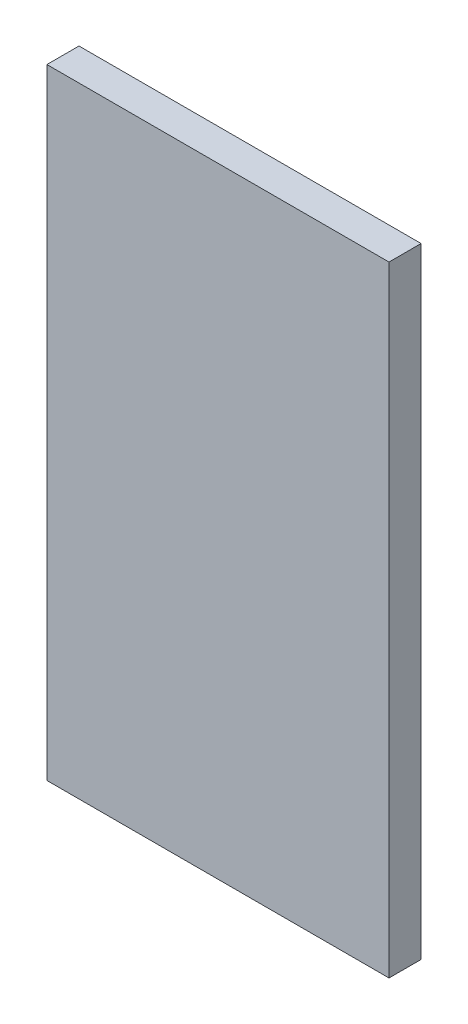
SolidWorks part; units mm, degrees
ref_plane "Plan de face" through (0, 0, 0) normal (0, 0, 1) x (1, 0, 0)
ref_plane "Plan de dessus" through (0, 0, 0) normal (0, 1, 0) x (1, 0, 0)
ref_plane "Plan de droite" through (0, 0, 0) normal (1, 0, 0) x (0, 0, -1)
sketch "Esquisse1" plane through (0, 0, 0) normal (0, 0, 1) x (1, 0, 0)
  line L1 (0, 0) -> (32, 0)
  line L2 (0, 0) -> (0, -58)
  line L3 (0, -58) -> (32, -58)
  line L4 (32, 0) -> (32, -58)
  dimension "D1" = 58
  dimension "D2" = 32
extrude "Boss.-Extru.1" add sketch "Esquisse1" along normal blind 3
